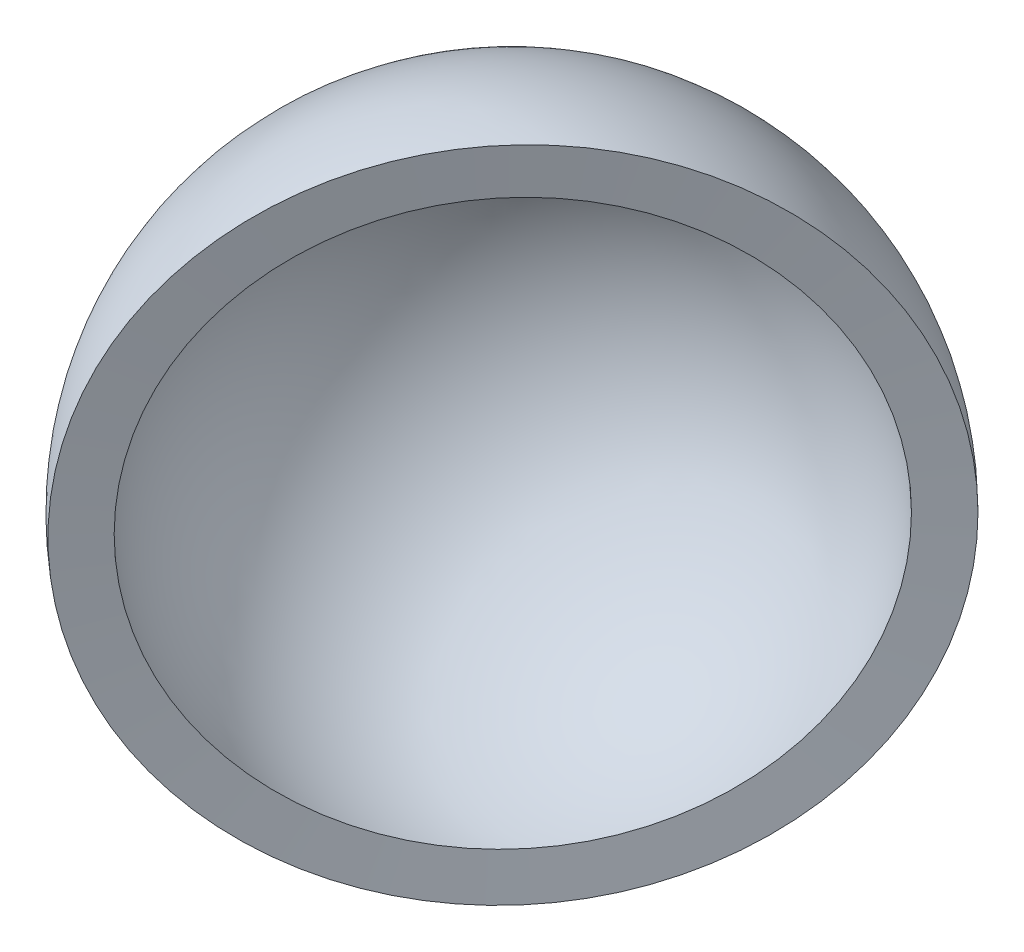
SolidWorks part; units mm, degrees
ref_plane "Alzado" through (0, 0, 0) normal (0, 0, 1) x (1, 0, 0)
ref_plane "Planta" through (0, 0, 0) normal (0, 1, 0) x (1, 0, 0)
ref_plane "Vista lateral" through (0, 0, 0) normal (1, 0, 0) x (0, 0, -1)
sketch "Croquis1" plane through (0, 0, 0) normal (0, 1, 0) x (1, 0, 0)
  line L0 (-7.3967, 6.7297) -> (-8.6285, 7.8505)
  line L1 (-8.6285, 7.8505) -> (-8.631, 7.8529)
  line L2 (7.0711, 7.0711) -> (8.2486, 8.2486)
  line L3 (-8.2841, 8.213) -> (-8.2867, 8.2155)
  line L4 (-8.2867, 8.2155) -> (-8.631, 7.8529)
  arc A0 (7.0711, 7.0711) -> (-7.3967, 6.7297) centre (0, 0) ccw
  arc A1 (8.2486, 8.2486) -> (-8.2841, 8.213) centre (0, 0) ccw
  dimension "D1" = 0.5
revolve "Revolución1" add sketch "Croquis1" angle 360 about L0
